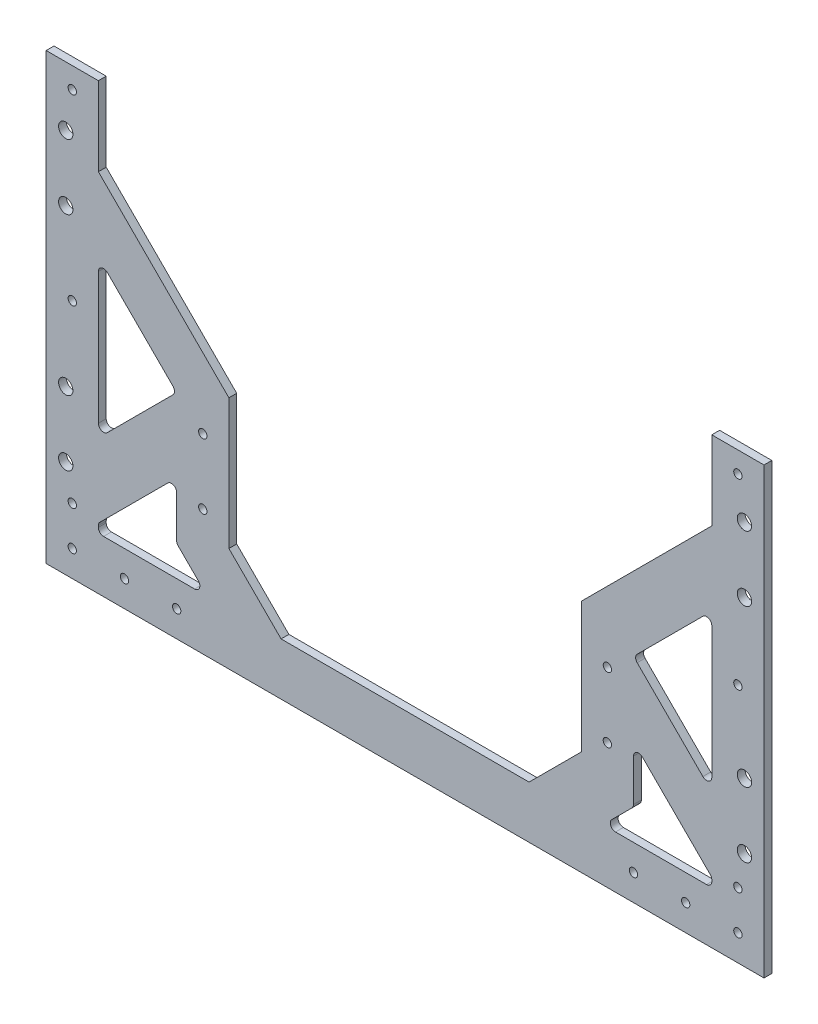
SolidWorks part; units mm, degrees
material "Thornel Mat VMA"
ref_plane "Front Plane" through (0, 0, 0) normal (0, 0, 1) x (1, 0, 0)
ref_plane "Top Plane" through (0, 0, 0) normal (0, 1, 0) x (1, 0, 0)
ref_plane "Right Plane" through (0, 0, 0) normal (1, 0, 0) x (0, 0, -1)
sketch "Sketch1" plane through (0, 0, 0) normal (0, 0, 1) x (1, 0, 0)
  line L0 (-21.5101, 142.7096) -> (-21.5101, -27.503)
  line L1 (-21.5101, 592.497) -> (-21.5101, 302.497) construction
  line L2 (-171.5101, -27.503) -> (403.4899, -27.503) construction
  line L3 (-21.5101, -27.503) -> (253.4899, -27.503)
  line L4 (253.4899, -27.503) -> (253.4899, 142.7096)
  line L5 (253.4899, -7.503) -> (253.4899, 282.497) construction
  line L6 (253.4899, 142.7096) -> (233.4899, 142.7096)
  line L7 (233.4899, -7.503) -> (233.4899, 282.497) construction
  line L8 (233.4899, 142.7096) -> (233.4899, 112.497)
  line L9 (233.4899, 112.497) -> (183.4899, 62.497)
  line L10 (183.4899, 62.497) -> (183.4899, 12.497)
  line L11 (183.4899, 12.497) -> (163.4899, -7.503)
  line L12 (-1.5101, -7.503) -> (233.4899, -7.503) construction
  line L13 (163.4899, -7.503) -> (68.4899, -7.503)
  line L14 (115.9899, -7.503) -> (115.9899, 82.0954) construction
  line L15 (48.4899, 12.497) -> (68.4899, -7.503)
  line L16 (48.4899, 62.497) -> (48.4899, 12.497)
  line L17 (-1.5101, 112.497) -> (48.4899, 62.497)
  line L18 (-1.5101, 142.7096) -> (-1.5101, 112.497)
  line L19 (-21.5101, 142.7096) -> (-1.5101, 142.7096)
  line L20 (-1.5101, 592.497) -> (-1.5101, 302.497) construction
  line L21 (233.4899, -7.503) -> (233.4899, 282.497) construction
  line L22 (-1.5101, -7.503) -> (233.4899, -7.503) construction
  line L23 (-1.5101, -5.503) -> (-1.5101, -4.8999)
  line L24 (1.9041, 80.7986) -> (27.0757, 55.627)
  line L25 (28.4899, 21.1001) -> (28.4899, 5.0412)
  line L26 (29.0757, 3.627) -> (36.7914, -4.0887)
  line L27 (35.3772, -7.503) -> (0.4899, -7.503)
  line L28 (27.0757, 52.7986) -> (1.9041, 27.627)
  line L29 (233.4899, 29.0412) -> (233.4899, 79.3843)
  line L30 (-0.9243, -3.4857) -> (25.0757, 22.5143)
  line L31 (-1.5101, 29.0412) -> (-1.5101, 79.3843)
  line L32 (230.0757, 80.7986) -> (204.9041, 55.627)
  line L33 (232.9041, -3.4857) -> (206.9041, 22.5143)
  line L34 (204.9041, 52.7986) -> (230.0757, 27.627)
  line L35 (196.6026, -7.503) -> (231.4899, -7.503)
  line L36 (202.9041, 3.627) -> (195.1884, -4.0887)
  line L37 (203.4899, 21.1001) -> (203.4899, 5.0412)
  line L38 (233.4899, -5.503) -> (233.4899, -4.8999)
  arc A0 (36.7914, -4.0887) -> (35.3772, -7.503) centre (35.3772, -5.503) cw
  arc A1 (28.4899, 5.0412) -> (29.0757, 3.627) centre (30.4899, 5.0412) ccw
  arc A2 (25.0757, 22.5143) -> (28.4899, 21.1001) centre (26.4899, 21.1001) cw
  arc A3 (-1.5101, 79.3843) -> (1.9041, 80.7986) centre (0.4899, 79.3843) cw
  arc A4 (27.0757, 55.627) -> (27.0757, 52.7986) centre (25.6615, 54.2128) cw
  arc A5 (1.9041, 27.627) -> (-1.5101, 29.0412) centre (0.4899, 29.0412) cw
  arc A6 (-1.5101, -4.8999) -> (-0.9243, -3.4857) centre (0.4899, -4.8999) cw
  arc A7 (-1.5101, -5.503) -> (0.4899, -7.503) centre (0.4899, -5.503) ccw
  arc A8 (233.4899, 79.3843) -> (230.0757, 80.7986) centre (231.4899, 79.3843) ccw
  arc A9 (233.4899, -5.503) -> (231.4899, -7.503) centre (231.4899, -5.503) cw
  arc A10 (233.4899, -4.8999) -> (232.9041, -3.4857) centre (231.4899, -4.8999) ccw
  arc A11 (230.0757, 27.627) -> (233.4899, 29.0412) centre (231.4899, 29.0412) ccw
  arc A12 (204.9041, 55.627) -> (204.9041, 52.7986) centre (206.3183, 54.2128) ccw
  arc A13 (206.9041, 22.5143) -> (203.4899, 21.1001) centre (205.4899, 21.1001) ccw
  arc A14 (203.4899, 5.0412) -> (202.9041, 3.627) centre (201.4899, 5.0412) cw
  arc A15 (195.1884, -4.0887) -> (196.6026, -7.503) centre (196.6026, -5.503) ccw
  point P41 (28.4899, 4.6429)
  point P44 (40.2056, -7.503)
  point P55 (-1.5101, 24.2128)
  point P60 (-1.5101, -7.503)
  dimension "D10" = 2
  dimension "D1" = 20
  dimension "D2" = 45
  dimension "D3" = 50
  dimension "D4" = 20
  dimension "D5" = 50
  dimension "D6" = 20
  dimension "D7" = 20
  dimension "D8" = 20
  dimension "D9" = 45
extrude "Extrude1" add sketch "Sketch1" along normal blind 3
sketch "Sketch2" plane through (0, 0, 3) normal (0, 0, 1) x (1, 0, 0)
  line L0 (-11.5101, 142.7096) -> (-11.5101, -27.503) construction
  line L1 (-1.5101, 142.7096) -> (-21.5101, 142.7096) construction
  line L2 (-21.5101, -27.503) -> (253.4899, -27.503) construction
  line L3 (115.9899, -7.503) -> (115.9899, -27.503) construction
  line L4 (-1.5101, -7.503) -> (233.4899, -7.503) construction
  line L5 (-221.5101, -27.503) -> (453.4899, -27.503) construction
  line L6 (-21.5101, -17.503) -> (115.9899, -17.503) construction
  line L7 (-21.5101, 142.7096) -> (-21.5101, -27.503) construction
  line L8 (68.4899, 20.5695) -> (38.4899, 20.5695) construction
  line L9 (68.4899, 45.5695) -> (38.4899, 45.5695) construction
  line L10 (38.4899, 20.5695) -> (38.4899, 45.5695) construction
  line L11 (48.4899, 12.497) -> (48.4899, 62.497) construction
  circle A0 centre (245.9899, 9.9974) radius 2.75 construction
  circle A1 centre (245.9899, 34.9974) radius 2.75 construction
  circle A2 centre (245.9899, 94.9974) radius 2.75 construction
  circle A3 centre (245.9899, 119.9974) radius 2.75 construction
  circle A4 centre (-14.0101, 9.9974) radius 2.75 construction
  circle A5 centre (-14.0101, 34.9974) radius 2.75 construction
  circle A6 centre (-14.0101, 94.9974) radius 2.75 construction
  circle A7 centre (-14.0101, 119.9974) radius 2.75 construction
  circle A8 centre (245.9899, 9.9974) radius 2.75
  circle A9 centre (245.9899, 34.9974) radius 2.75
  circle A10 centre (245.9899, 94.9974) radius 2.75
  circle A11 centre (245.9899, 119.9974) radius 2.75
  circle A12 centre (-14.0101, 9.9974) radius 2.75
  circle A13 centre (-14.0101, 34.9974) radius 2.75
  circle A14 centre (-14.0101, 94.9974) radius 2.75
  circle A15 centre (-14.0101, 119.9974) radius 2.75
  circle A16 centre (-11.5101, 134.7096) radius 1.6
  circle A17 centre (-11.5101, 64.7096) radius 1.6
  circle A18 centre (-11.5101, -2.503) radius 1.6
  circle A19 centre (-11.5101, -17.503) radius 1.6
  circle A20 centre (8.4899, -17.503) radius 1.6
  circle A21 centre (28.4899, -17.503) radius 1.6
  circle A22 centre (203.4899, -17.503) radius 1.6
  circle A23 centre (223.4899, -17.503) radius 1.6
  circle A24 centre (243.4899, -17.503) radius 1.6
  circle A25 centre (243.4899, -2.503) radius 1.6
  circle A26 centre (243.4899, 64.7096) radius 1.6
  circle A27 centre (243.4899, 134.7096) radius 1.6
  circle A28 centre (245.9899, 119.9974) radius 2.75
  circle A29 centre (245.9899, 94.9974) radius 2.75
  circle A30 centre (245.9899, 34.9974) radius 2.75
  circle A31 centre (245.9899, 9.9974) radius 2.75
  circle A32 centre (38.4899, 20.5695) radius 1.6
  circle A33 centre (38.4899, 45.5695) radius 1.6
  circle A34 centre (193.4899, 45.5695) radius 1.6
  circle A35 centre (193.4899, 20.5695) radius 1.6
  point P82 (0, 0)
  point P83 (0, 0)
  dimension "D1" = 3.2
  dimension "D3" = 70
  dimension "D4" = 15
  dimension "D5" = 20
  dimension "D6" = 20
  dimension "D8" = 3.2
  dimension "D2" = 8
  dimension "D7" = 10
extrude "Cut-Extrude1" cut sketch "Sketch2" against normal blind 3 contours A15 | A14 | A13 | A12 | A18 | A19 | A20 | A21 | A32 | A33 | A17 | A34 | A35 | A22 | A23 | A24 | A9 | A8 | A26 | A27 | A11 | A10 | A16 | A25
